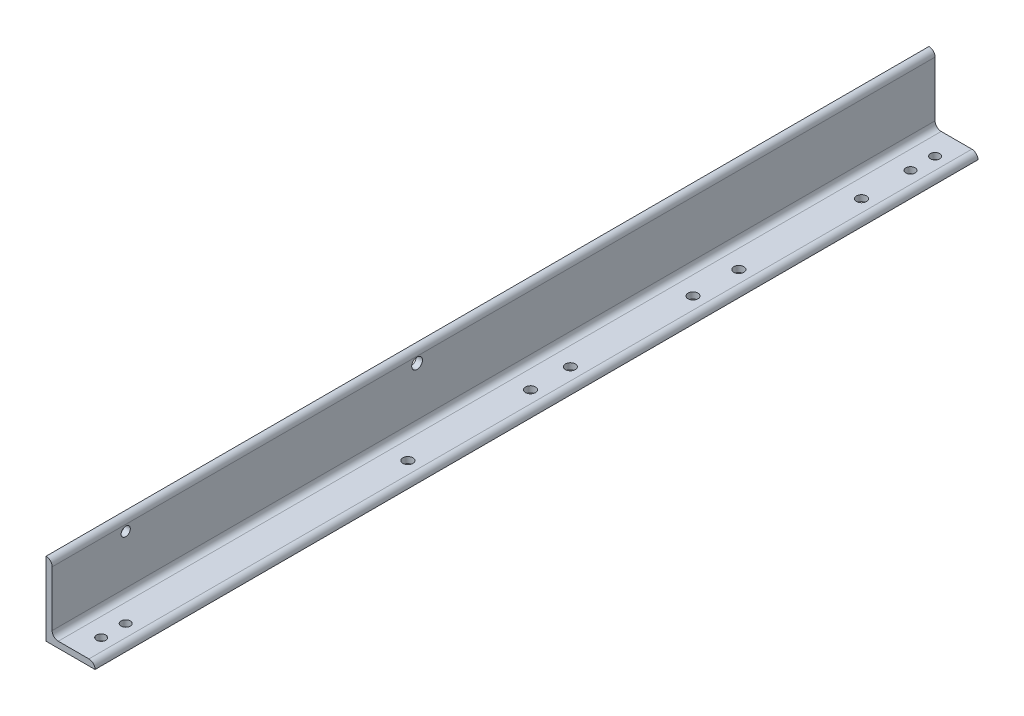
SolidWorks part; units mm, degrees
ref_plane "Front Plane" through (0, 0, 0) normal (0, 0, 1) x (1, 0, 0)
ref_plane "Top Plane" through (0, 0, 0) normal (0, 1, 0) x (1, 0, 0)
ref_plane "Right Plane" through (0, 0, 0) normal (1, 0, 0) x (0, 0, -1)
sketch "Sketch1" plane through (0, 0, 0) normal (0, 0, 1) x (1, 0, 0)
  line L0 (0, 0) -> (0, 152.4)
  line L1 (0, 152.4) -> (0.0051, 152.4)
  line L2 (12.7, 139.7051) -> (12.7, 25.4)
  line L3 (25.4, 12.7) -> (88.9051, 12.7)
  line L4 (101.6, 0.0051) -> (101.6, 0)
  line L5 (101.6, 0) -> (0, 0)
  arc A0 (101.6, 0.0051) -> (88.9051, 12.7) centre (88.9051, 0.0051) ccw
  arc A1 (0.0051, 152.4) -> (12.7, 139.7051) centre (0.0051, 139.7051) cw
  arc A2 (25.4, 12.7) -> (12.7, 25.4) centre (25.4, 25.4) cw
  circle A3 centre (0, 0) radius 12.7 construction
  dimension "D2" = 0.0051
  dimension "Radius_1" = 12.7
  dimension "Radius_2" = 12.7
  dimension "D1" = 12.7
  dimension "V_leg" = 152.4
  dimension "H_leg" = 101.6
  dimension "Thickness" = 12.7
  dimension "Flat_wid" = 0.0051
extrude "Boss-Extrude1" add sketch "Sketch1" along normal mid plane 1828.8
sketch "Sketch3" plane through (0, 12.7, 0) normal (0, 1, 0) x (1, 0, 0)
  line L0 (63.5, -964.9914) -> (63.5, 988.9202) construction
  line L1 (101.6, -914.4) -> (101.6, 914.4) construction
  line L2 (88.9051, -914.4) -> (25.4, -914.4) construction
  line L3 (88.9051, 914.4) -> (25.4, 914.4) construction
  line L4 (63.5, -812.8) -> (88.9051, -812.8) construction
  line L5 (88.9051, -914.4) -> (88.9051, 914.4) construction
  circle A0 centre (63.5, -863.6) radius 9.525
  circle A1 centre (63.5, 863.6) radius 9.525
  circle A2 centre (63.5, 25.654) radius 10.3187
  circle A3 centre (63.5, -812.8) radius 9.525
  circle A4 centre (63.5, 711.2) radius 10.3187
  circle A5 centre (63.5, 457.2) radius 10.3188
  circle A6 centre (63.5, -228.346) radius 10.3187
  circle A7 centre (63.5, 362.204) radius 10.3188
  circle A8 centre (63.5, 108.204) radius 10.3188
  circle A9 centre (63.5, 812.8) radius 9.525
  dimension "D3" = 50.8
  dimension "D4" = 888.746
  dimension "D5" = 254
  dimension "D6" = 203.2
  dimension "D7" = 254
  dimension "D9" = 20.6375
  dimension "D10" = 254
  dimension "D11" = 552.196
  dimension "D8" = 50.8
  dimension "D12" = 50.8
  dimension "D1" = 38.1
  dimension "D2" = 50.8
extrude "Cut-Extrude2" cut sketch "Sketch3" against normal up to next
hole_wizard "3/4 (0.75) Diameter Hole1" positions "Sketch5" profile "Sketch4" hole size "3/4" standard "Ansi Inch" end condition up to next
sketch "Sketch5" plane through (12.7, 0, 0) normal (1, 0, 0) x (0, 0, -1)
  line L0 (-914.4, 25.4) -> (-914.4, 139.7051) construction
  line L1 (-914.4, 152.4) -> (914.4, 152.4) construction
  point P0 (-762, 127)
  dimension "D1" = 152.4
  dimension "D2" = 25.4
sketch "Sketch4" plane through (12.7, 127, 762) normal (0, 1, 0) x (0, 0, -1)
  line L0 (0, 0) -> (0, 12.7)
  line L1 (0, 12.7) -> (9.525, 12.7)
  line L2 (9.525, 12.7) -> (9.525, 0)
  line L5 (9.525, 0) -> (0, 0)
  line L11 (0, -6.35) -> (0, 107.95) construction
  dimension "Thru Hole Dia." = 19.05
  dimension "Thru Hole Depth" = 12.7
sketch "Sketch6" plane through (12.7, 0, 0) normal (1, 0, 0) x (0, 0, -1)
  line L0 (-914.4, 25.4) -> (-914.4, 139.7051) construction
  line L1 (-914.4, 152.4) -> (914.4, 152.4) construction
  circle A0 centre (-158.496, 127) radius 11.1125
  dimension "D1" = 755.904
  dimension "D2" = 25.4
extrude "Cut-Extrude3" cut sketch "Sketch6" against normal through all
equation "\"D3@Sketch3\" = \"D2@Sketch3\""
